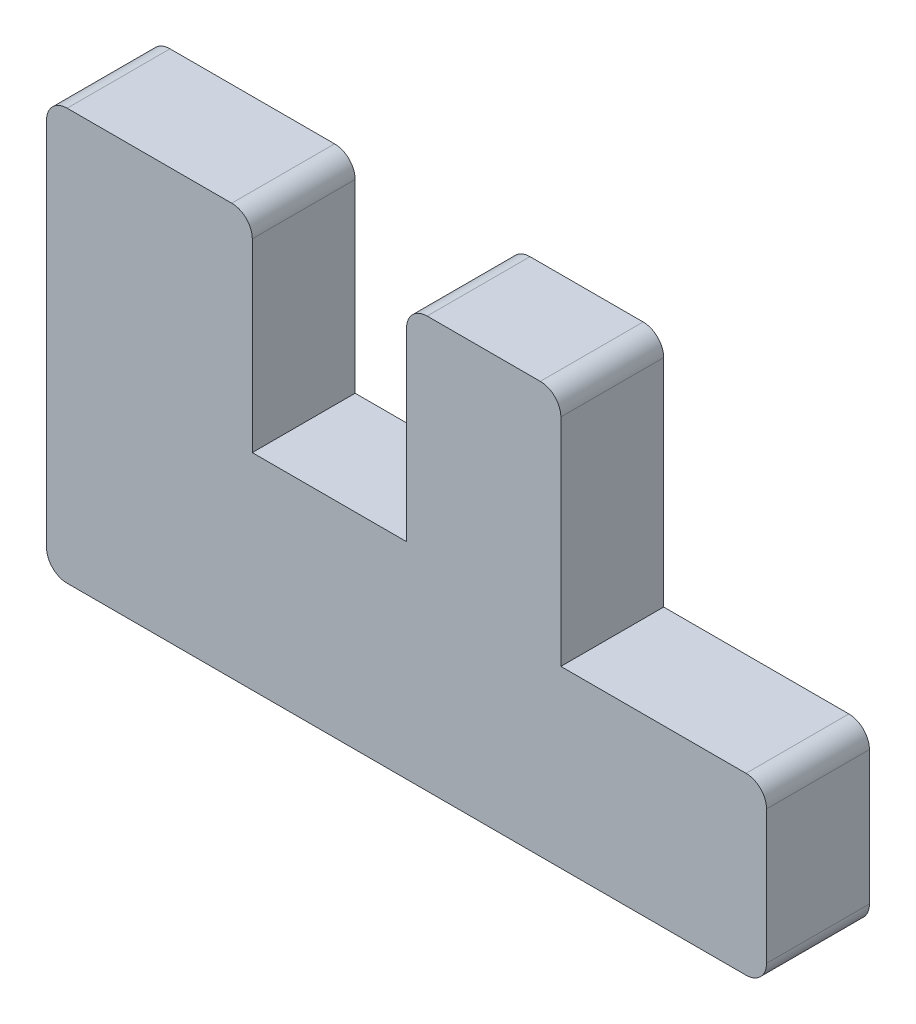
SolidWorks part; units mm, degrees
ref_plane "Front Plane" through (0, 0, 0) normal (0, 0, 1) x (1, 0, 0)
ref_plane "Top Plane" through (0, 0, 0) normal (0, 1, 0) x (1, 0, 0)
ref_plane "Right Plane" through (0, 0, 0) normal (1, 0, 0) x (0, 0, -1)
sketch "Sketch1" plane through (0, 0, 0) normal (0, 0, 1) x (1, 0, 0)
  line L0 (0, 0) -> (0, 50.8)
  line L1 (0, 0) -> (88.9, 0)
  line L2 (0, 50.8) -> (25.4, 50.8)
  line L3 (25.4, 50.8) -> (25.4, 25.4)
  line L4 (25.4, 25.4) -> (44.45, 25.4)
  line L5 (44.45, 25.4) -> (44.45, 50.8)
  line L6 (44.45, 50.8) -> (63.5, 50.8)
  line L7 (63.5, 50.8) -> (63.5, 21.59)
  line L11 (88.9, 0) -> (88.9, 21.59)
  line L12 (88.9, 21.59) -> (63.5, 21.59)
  dimension "D1" = 21.59
  dimension "D2" = 25.4
  dimension "D3" = 44.45
  dimension "D4" = 63.5
  dimension "D5" = 88.9
  dimension "D6" = 50.8
  dimension "D7" = 25.4
other "AlignGroup1"
extrude "Boss-Extrude1" add sketch "Sketch1" along normal blind 12.7
fillet "Fillet1" radius 2.54 7 edges at (88.9, 0, 6.35) (88.9, 21.59, 6.35) (0, 0, 6.35) (25.4, 50.8, 6.35) (63.5, 50.8, 6.35) (44.45, 50.8, 6.35) (0, 50.8, 6.35)
